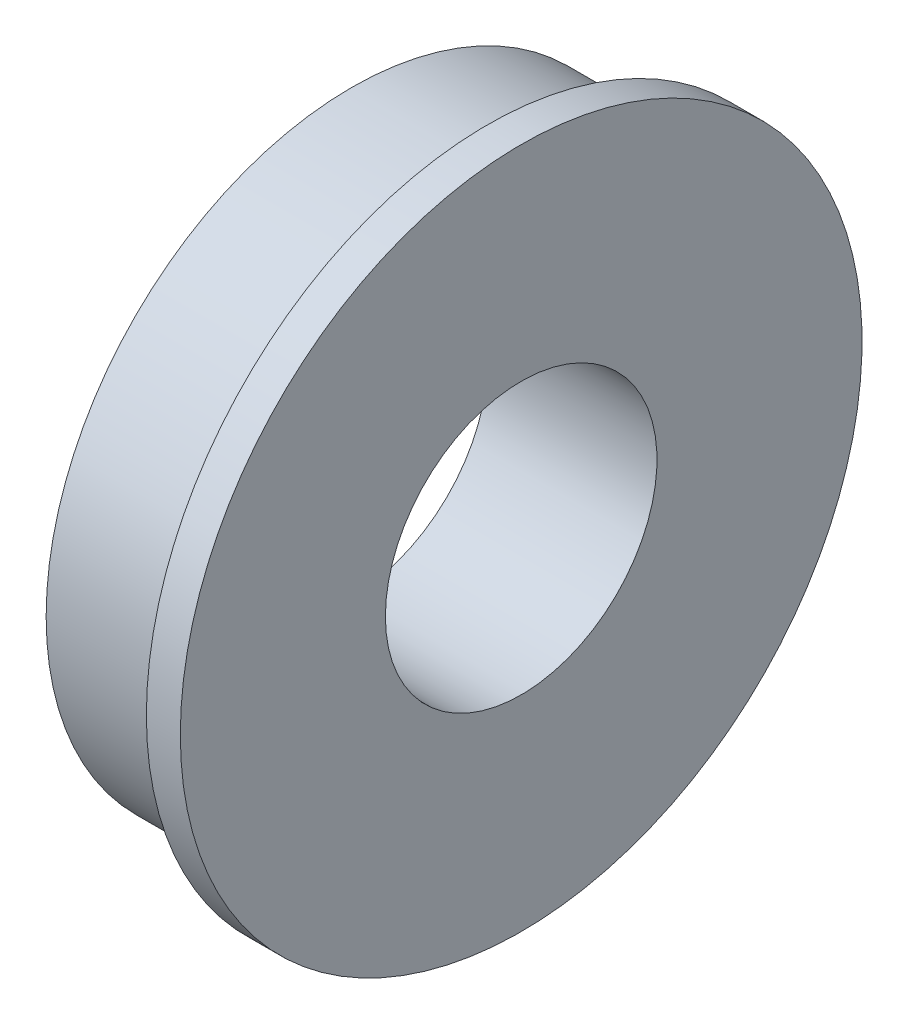
SolidWorks part; units mm, degrees
material "AISI 321 Annealed Stainless Steel (SS)"
ref_plane "Front Plane" through (0, 0, 0) normal (0, 0, 1) x (1, 0, 0)
ref_plane "Top Plane" through (0, 0, 0) normal (0, 1, 0) x (1, 0, 0)
ref_plane "Right Plane" through (0, 0, 0) normal (1, 0, 0) x (0, 0, -1)
sketch "Sketch1" plane through (0, 0, 0) normal (0, 0, 1) x (1, 0, 0)
  line L0 (0, 0) -> (7.9248, 0) construction
  line L1 (7.9248, 0) -> (7.9248, 6.35) construction
  line L2 (7.9248, 6.35) -> (0, 6.35)
  line L3 (0, 6.35) -> (0, 14.2875)
  line L4 (0, 14.2875) -> (6.3373, 14.2875)
  line L5 (6.3373, 14.2875) -> (6.3373, 15.9385)
  line L6 (6.3373, 15.9385) -> (7.9248, 15.9385)
  line L7 (7.9248, 15.9385) -> (7.9248, 6.35)
  dimension "D1" = 14.2875
  dimension "D2" = 6.35
  dimension "D3" = 1.5875
  dimension "D4" = 7.9248
  dimension "D5" = 15.9385
revolve "Revolve1" add sketch "Sketch1" angle 360 about L0
